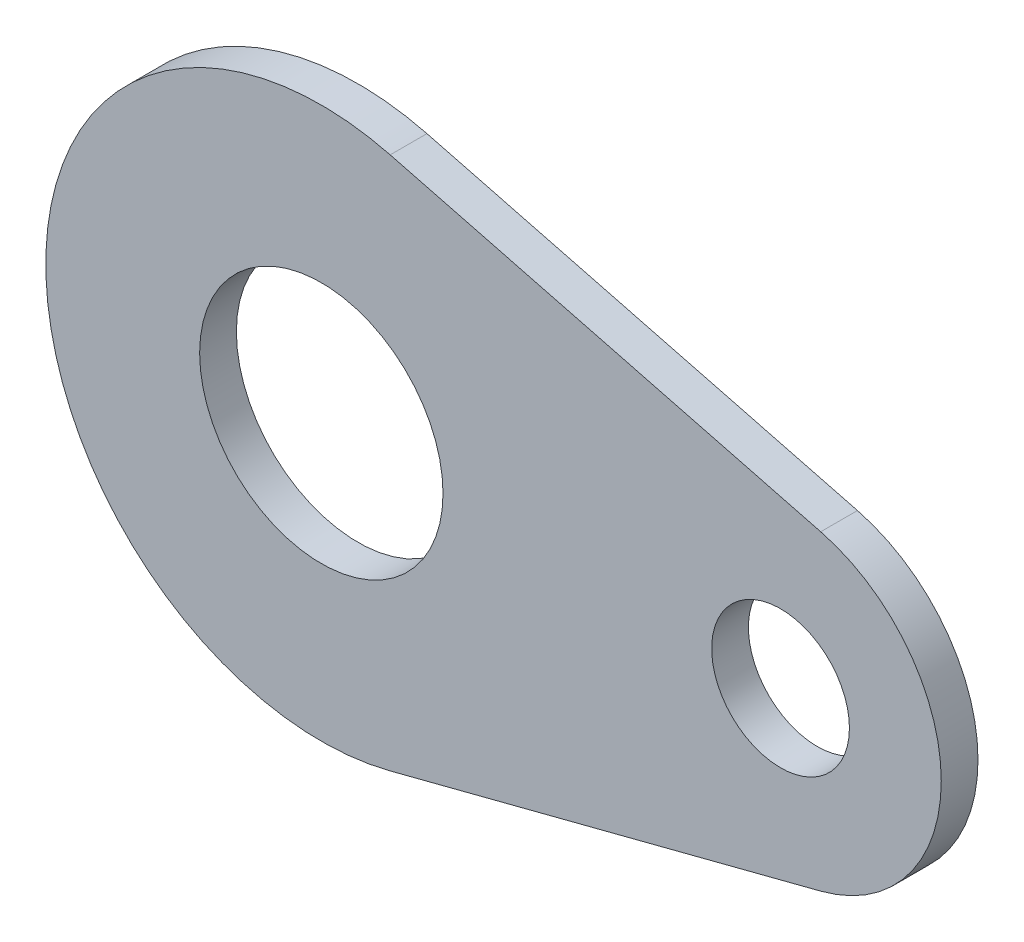
SolidWorks part; units mm, degrees
material "AISI 316 Stainless Steel Sheet (SS)"
ref_plane "Front" through (0, 0, 0) normal (0, 0, 1) x (1, 0, 0)
ref_plane "Top" through (0, 0, 0) normal (0, 1, 0) x (1, 0, 0)
ref_plane "Right" through (0, 0, 0) normal (1, 0, 0) x (0, 0, -1)
sketch "Sketch1" plane through (0, 0, 0) normal (0, 0, 1) x (1, 0, 0)
  line L0 (0, 0) -> (10, 0) construction
  line L1 (1.5, 5.8095) -> (10.875, 3.3889)
  line L2 (10.875, -3.3889) -> (1.5, -5.8095)
  circle A0 centre (0, 0) radius 2.65
  circle A1 centre (0, 0) radius 6 construction
  circle A2 centre (10, 0) radius 1.5
  circle A3 centre (10, 0) radius 3.5 construction
  arc A4 (10.875, 3.3889) -> (10.875, -3.3889) centre (10, 0) cw
  arc A5 (1.5, 5.8095) -> (1.5, -5.8095) centre (0, 0) ccw
  dimension "D1" = 5.3
  dimension "D2" = 12
  dimension "D3" = 3
  dimension "D4" = 7
  dimension "D5" = 10
extrude "Boss-Extrude1" add sketch "Sketch1" along normal blind 0.8
